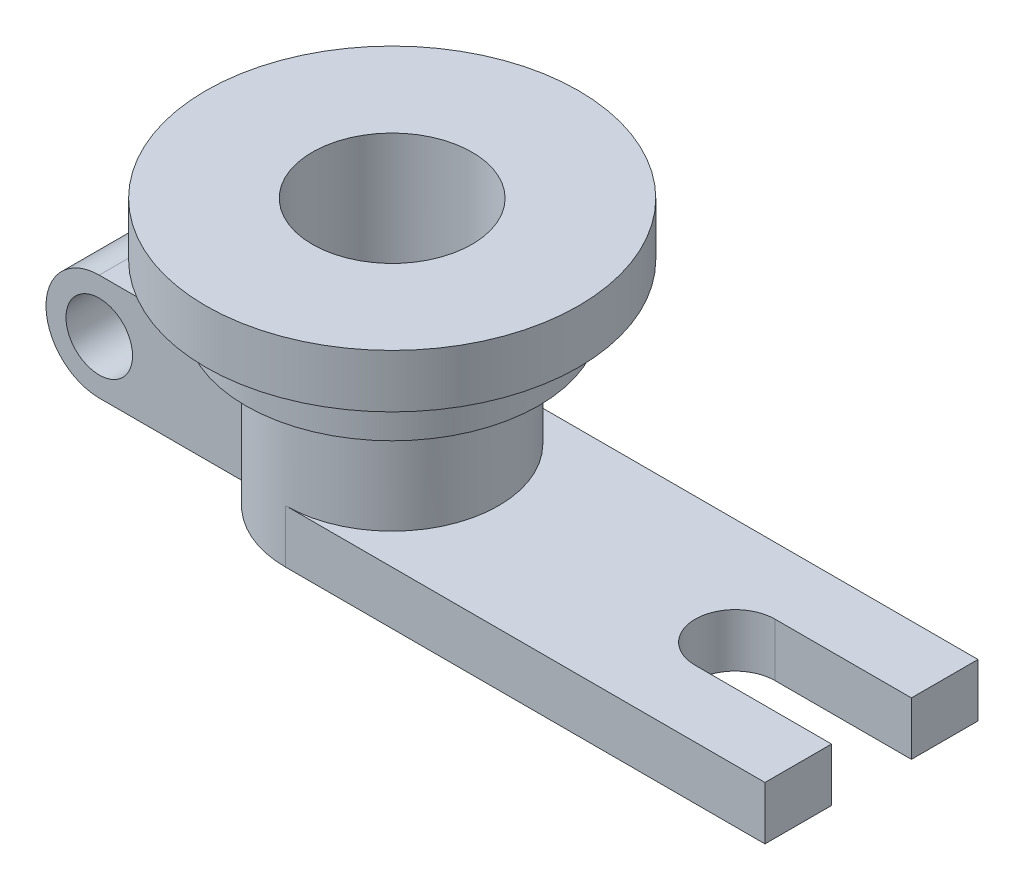
SolidWorks part; units mm, degrees
ref_plane "Front Plane" through (0, 0, 0) normal (0, 0, 1) x (1, 0, 0)
ref_plane "Top Plane" through (0, 0, 0) normal (0, 1, 0) x (1, 0, 0)
ref_plane "Right Plane" through (0, 0, 0) normal (1, 0, 0) x (0, 0, -1)
sketch "Sketch1" plane through (0, 0, 0) normal (0, 1, 0) x (1, 0, 0)
  circle A0 centre (0, 0) radius 55
  dimension "D1" = 110
extrude "Boss-Extrude1" add sketch "Sketch1" along normal blind 20
sketch "Sketch2" plane through (0, 20, 0) normal (0, 1, 0) x (1, 0, 0)
  circle A0 centre (0, 0) radius 70
  dimension "D1" = 140
extrude "Boss-Extrude2" add sketch "Sketch2" along normal blind 20
sketch "Sketch3" plane through (0, 0, 0) normal (0, -1, 0) x (1, 0, 0)
  circle A0 centre (0, 0) radius 40
  dimension "D1" = 80
extrude "Boss-Extrude3" add sketch "Sketch3" along normal blind 60
sketch "Sketch4" plane through (0, 40, 0) normal (0, 1, 0) x (1, 0, 0)
  circle A0 centre (0, 0) radius 30
  dimension "D1" = 60
extrude "Cut-Extrude1" cut sketch "Sketch4" against normal up to next
ref_plane "Plane1" through (180, 0, 0) normal (1, 0, 0) x (0, 0, -1)
sketch "Sketch6" plane through (180, 0, 0) normal (1, 0, 0) x (0, 0, -1)
  line L0 (40, -60) -> (40, 0) construction
  line L1 (-40, -40) -> (40, -40)
  line L2 (-40, -40) -> (-40, -60)
  line L3 (-40, -60) -> (40, -60)
  line L4 (40, -40) -> (40, -60)
  line L5 (-40, -40) -> (40, -60) construction
  line L6 (-40, -60) -> (40, -40) construction
  line L7 (-40, -60) -> (40, -60) construction
  point P0 (0, -50)
  point P5 (40, -50)
  dimension "D1" = 20
  dimension "D2" = 80
  dimension "D3" = 0
  dimension "D4" = 0
extrude "Boss-Extrude4" add sketch "Sketch6" against normal up to surface (180 mm away) up to face at (0, -60, -40)
sketch "Sketch8" plane through (0, -40, 0) normal (0, 1, 0) x (1, 0, 0)
  line L0 (180, 15) -> (180, -15)
  line L1 (128.7735, 15) -> (180, 15)
  line L2 (128.7735, -15) -> (180, -15)
  arc A0 (128.7735, 15) -> (128.7735, -15) centre (128.7735, 0) ccw
  dimension "D1" = 30
extrude "Cut-Extrude2" cut sketch "Sketch8" against normal blind 60
ref_plane "Plane2" through (-110, 0, 0) normal (1, 0, 0) x (0, 0, -1)
sketch "Sketch10" plane through (-110, 0, 0) normal (1, 0, 0) x (0, 0, -1)
  line L0 (-40, -60) -> (40, -60) construction
  line L1 (20, -20) -> (-20, -20)
  line L2 (20, -20) -> (20, -60)
  line L3 (20, -60) -> (-20, -60)
  line L4 (-20, -20) -> (-20, -60)
  line L5 (20, -20) -> (-20, -60) construction
  line L6 (20, -60) -> (-20, -20) construction
  line L7 (0, 113.7687) -> (0, -107.3714) construction
  point P0 (0, -40)
  dimension "D1" = 40
  dimension "D2" = 40
  dimension "D3" = 0
  dimension "D4" = 20
extrude "Boss-Extrude5" add sketch "Sketch10" along normal up to surface (75.359 mm away)
sketch "Sketch11" plane through (0, 0, 20) normal (0, 0, 1) x (1, 0, 0)
  line L0 (-110, -20) -> (-110, -60) construction
  line L5 (-90, -20) -> (-110, -20)
  line L6 (-110, -20) -> (-110, -60)
  line L7 (-110, -60) -> (-90, -60)
  arc A0 (-90, -20) -> (-90, -60) centre (-90, -40) ccw
  point P4 (-110, -40)
  line M2 (-34.641, -20) -> (-110, -20)
  line M3 (-110, -20) -> (-110, -60)
  line M4 (-110, -60) -> (-34.641, -60)
  dimension "D2" = 20
extrude "Cut-Extrude3" cut sketch "Sketch11" against normal blind 60 contours A0 M2 M3 | A0 L6 M4
sketch "Sketch12" plane through (0, 0, 20) normal (0, 0, 1) x (1, 0, 0)
  circle A0 centre (-90, -40) radius 12.5
  dimension "D1" = 25
extrude "Cut-Extrude4" cut sketch "Sketch12" against normal blind 60
